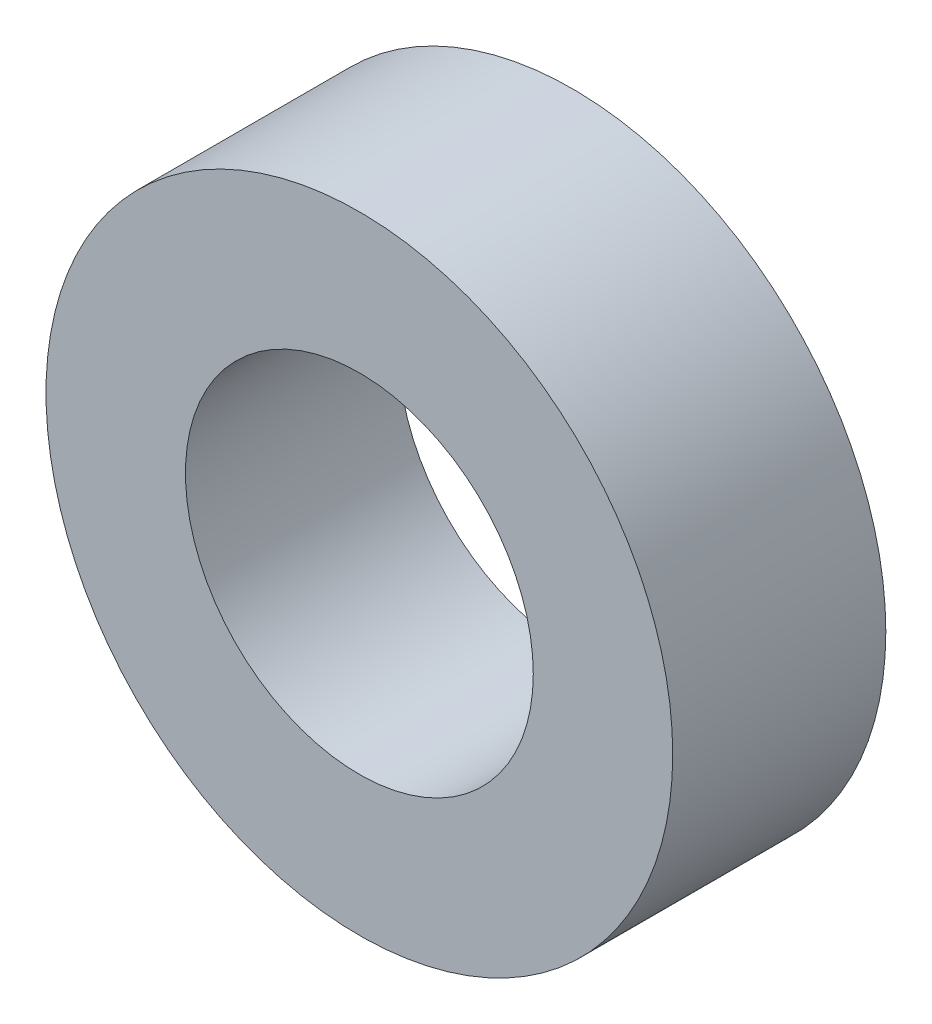
SolidWorks part; units mm, degrees
ref_plane "Front Plane" through (0, 0, 0) normal (0, 0, 1) x (1, 0, 0)
ref_plane "Top Plane" through (0, 0, 0) normal (0, 1, 0) x (1, 0, 0)
ref_plane "Right Plane" through (0, 0, 0) normal (1, 0, 0) x (0, 0, -1)
sketch "Sketch1" plane through (0, 0, 0) normal (0, 0, 1) x (1, 0, 0)
  circle A0 centre (0, 0) radius 5.55
  circle A1 centre (0, 0) radius 10
  dimension "D1" = 20
  dimension "D2" = 11.1
extrude "Boss-Extrude1" add sketch "Sketch1" along normal blind 6.8
